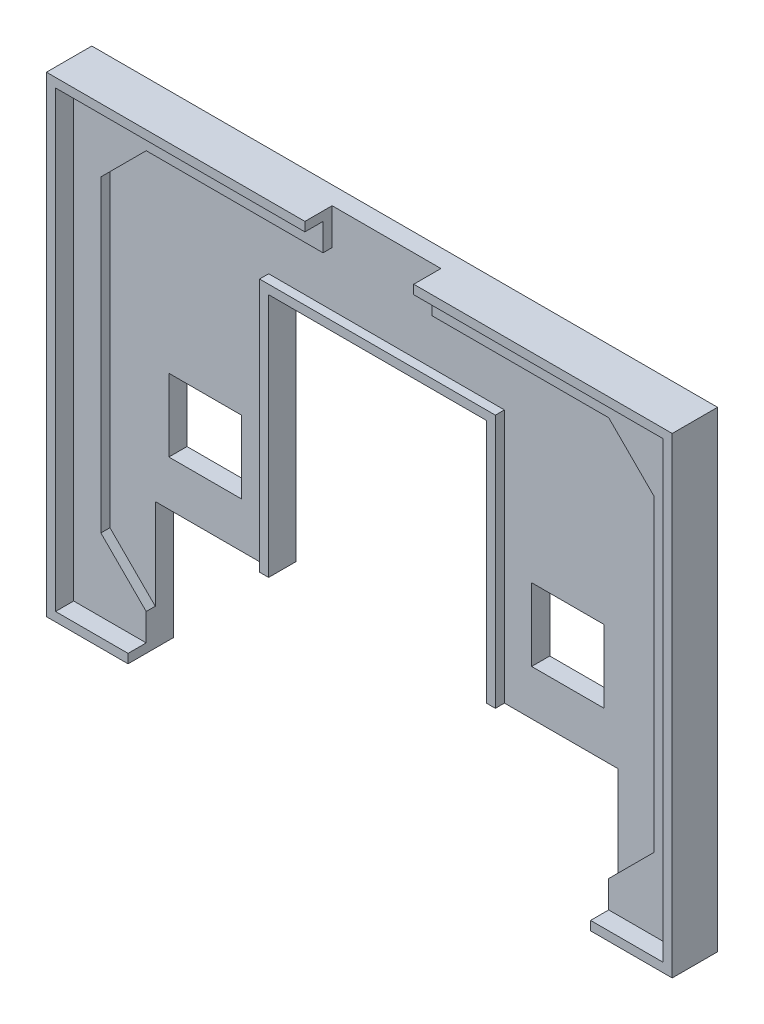
SolidWorks part; units mm, degrees
ref_plane "Přední rovina" through (0, 0, 0) normal (0, 0, 1) x (1, 0, 0)
ref_plane "Horní rovina" through (0, 0, 0) normal (0, 1, 0) x (1, 0, 0)
ref_plane "Pravá rovina" through (0, 0, 0) normal (1, 0, 0) x (0, 0, -1)
sketch "Skica1" plane through (0, 0, 0) normal (0, 0, 1) x (1, 0, 0)
  line L1 (-33.5, -25) -> (33.5, -25)
  line L2 (-33.5, -25) -> (-33.5, 25)
  line L3 (-33.5, 25) -> (33.5, 25)
  line L4 (33.5, -25) -> (33.5, 25)
  line L5 (-33.5, -25) -> (33.5, 25) construction
  line L6 (-33.5, 25) -> (33.5, -25) construction
  point P0 (0, 0)
  dimension "D1" = 67
  dimension "D2" = 50
extrude "Přidat vysunutím1" add sketch "Skica1" along normal blind 3
sketch "Skica2" plane through (0, 0, 3) normal (0, 0, 1) x (1, 0, 0)
  line L0 (-1000, 0) -> (49000, 0) construction
  line L1 (0, -1000) -> (0, 49000) construction
  line L2 (-1000, -22) -> (49000, -22) construction
  line L3 (-25.5, -1000) -> (-25.5, 49000) construction
  line L4 (-30.5, -1000) -> (-30.5, 49000) construction
  line L6 (-33.5, -25) -> (33.5, -25) construction
  line L7 (-25.5, -22) -> (-30.5, -17)
  line L8 (-30.5, -17) -> (-30.5, 17)
  line L9 (-25.5, -22) -> (25.5, -22)
  line L10 (30.5, -17) -> (30.5, 17)
  line L11 (25.5, -22) -> (30.5, -17)
  line L12 (25.5, 22) -> (30.5, 17)
  line L13 (-25.5, 22) -> (25.5, 22)
  line L14 (-25.5, 22) -> (-30.5, 17)
  point P20 (0, -22)
  point P21 (30.5, 0)
  point P24 (-30.5, 0)
  dimension "D1" = 30.5
  dimension "D2" = 5
  dimension "D3" = 3
  dimension "D4" = 45
extrude "Odebrat vysunutím1" cut sketch "Skica2" against normal offset from surface (1 mm away) 2 up to face at (0, 0, 0)
sketch "Skica3" plane through (0, 0, 0) normal (0, 0, -1) x (-1, 0, 0)
  line L0 (0, -1000) -> (0, 49000) construction
  line L1 (33.5, -25) -> (-33.5, -25) construction
  line L2 (24, 1) -> (16, 1)
  line L3 (24, 1) -> (24, -7)
  line L4 (24, -7) -> (16, -7)
  line L5 (16, 1) -> (16, -7)
  line L6 (-16, 1) -> (-16, -7)
  line L7 (33.5, -25) -> (-33.5, -25) construction
  line L8 (25.5, -25) -> (-25.5, -25)
  line L9 (25.5, -25) -> (25.5, -12)
  line L11 (-25.5, -25) -> (-25.5, -12)
  line L12 (-24, -7) -> (-16, -7)
  line L13 (25.5, -12) -> (12, -12)
  line L15 (12, -12) -> (12, 15)
  line L16 (12, 15) -> (-12, 15)
  line L17 (-12, -12) -> (-12, 15)
  line L18 (-12, -12) -> (-25.5, -12)
  line L19 (-24, 1) -> (-24, -7)
  line L20 (-24, 1) -> (-16, 1)
  dimension "D1" = 16
  dimension "D2" = 8
  dimension "D3" = 18
  dimension "D4" = 13
  dimension "D5" = 51
  dimension "D6" = 24
  dimension "D7" = 27
extrude "Odebrat vysunutím2" cut sketch "Skica3" against normal through all
sketch "Skica4" plane through (0, 0, 2) normal (0, 0, 1) x (1, 0, 0)
  line L0 (12, 15) -> (12, -12) construction
  line L1 (-12, -12) -> (-12, 15) construction
  line L2 (-12, 15) -> (12, 15) construction
  line L3 (12, 15) -> (12, -12)
  line L4 (-12, -12) -> (-12, 15)
  line L5 (-12, 15) -> (12, 15)
extrude "Vysunout tenkostěnný1" add sketch "Skica4" along normal up to surface (1 mm away) thin up to face at (0, -3.5714, 3) thin type one direction reverse wall 1
sketch "Skica5" plane through (0, 0, 0) normal (0, 0, -1) x (-1, 0, 0)
  line L0 (-33.5, 25) -> (33.5, 25) construction
  line L1 (33.5, 25) -> (33.5, -25) construction
  line L2 (33.5, -25) -> (25.5, -25) construction
  line L3 (-33.5, -25) -> (-33.5, 25) construction
  line L4 (-25.5, -25) -> (-33.5, -25) construction
  line L5 (-33.5, 25) -> (33.5, 25)
  line L6 (33.5, 25) -> (33.5, -25)
  line L7 (33.5, -25) -> (25.5, -25)
  line L8 (-33.5, -25) -> (-33.5, 25)
  line L9 (-25.5, -25) -> (-33.5, -25)
extrude "Vysunout tenkostěnný2" add sketch "Skica5" against normal blind 5 thin thin type one direction reverse wall 1
sketch "Skica6" plane through (0, 0, 2) normal (0, 0, 1) x (1, 0, 0)
  line L0 (0, -1000) -> (0, 49000) construction
  line L1 (25.5, 22) -> (-25.5, 22) construction
  line L2 (-6, 22) -> (6, 22)
  line L3 (-6, 22) -> (-6, 26)
  line L4 (-6, 26) -> (6, 26)
  line L5 (6, 22) -> (6, 26)
  line L6 (34.5, 26) -> (-34.5, 26) construction
  dimension "D1" = 12
extrude "Odebrat vysunutím3" cut sketch "Skica6" along normal through all
sketch "Skica7" plane through (0, 0, 0) normal (0, 0, -1) x (-1, 0, 0)
  line L0 (-412.4785, -204.4844) -> (-71.1451, -204.4844) construction
  line L1 (-32.44, 14.5405) -> (-23.4595, 23.94)
  line L2 (-23.4595, 23.94) -> (-14.06, 14.9595)
  line L3 (-14.06, 14.9595) -> (-23.0405, 5.56)
  line L4 (-23.0405, 5.56) -> (-32.44, 14.5405)
  line L5 (-34.5, 26) -> (34.5, 26) construction
  line L6 (0, 0) -> (0, 28.27) construction
  line L7 (-34.5, -26) -> (-34.5, 26) construction
  line L8 (14.06, 14.9595) -> (23.0405, 5.56)
  line L9 (23.4595, 23.94) -> (14.06, 14.9595)
  line L10 (32.44, 14.5405) -> (23.4595, 23.94)
  line L11 (23.0405, 5.56) -> (32.44, 14.5405)
  dimension "D1" = 13
  dimension "D2" = 13
  dimension "D3" = 2.06
  dimension "D4" = 2.06
  dimension "D5" = 2.06
extrude "Odebrat vysunutím5" cut sketch "Skica7" against normal blind 1
sketch "Skica8" plane through (0, 0, 0) normal (0, 0, -1) x (-1, 0, 0)
  line L4 (-32.44, 14.5405) -> (-23.0405, 5.56) construction
  line L5 (-23.4595, 23.94) -> (-32.44, 14.5405) construction
  line L10 (-14.06, 14.9595) -> (-23.4595, 23.94) construction
  line L16 (-32.44, 14.5405) -> (-23.0405, 5.56) construction
  line L17 (0, 0) -> (0, 28.374) construction
  line L30 (-29.2669, 14.9665) -> (-25.7669, 15.0801)
  line L31 (-23.7033, 17.2576) -> (-23.7476, 20.7576)
  line L47 (29.2669, 14.9665) -> (25.7669, 15.0801)
  line L48 (23.7033, 17.2576) -> (23.7476, 20.7576)
  spline S0 degree 2 poles (-29.2669, 14.9665) (-27.3984, 11.3649) (-25.7669, 15.0801) knots 0 0 0 1 1 1
  spline S1 degree 2 poles (-23.7033, 17.2576) (-20.0638, 19.0473) (-23.7476, 20.7576) knots 0 0 0 1 1 1
  spline S2 degree 2 poles (29.2669, 14.9665) (27.3984, 11.3649) (25.7669, 15.0801) knots 0 0 0 1 1 1
  spline S3 degree 2 poles (23.7033, 17.2576) (20.0638, 19.0473) (23.7476, 20.7576) knots 0 0 0 1 1 1
  dimension "D7" = 5.3
  dimension "D9" = 5.3
  dimension "D17" = 5
  dimension "D2" = 2.5
  dimension "D3" = 2
  dimension "D4" = 3.5
  dimension "D5" = 3.5
  dimension "D6" = 3
  dimension "D8" = 2.5
  dimension "D16" = 8
sketch "Skica11" plane through (0, 0, 0) normal (0, 0, -1) x (-1, 0, 0)
  line L0 (-25.7245, 9.2308) -> (-24.692, 9.8422)
  line L1 (-24.692, 9.8422) -> (-24.9875, 11.7191)
  line L2 (-24.9875, 11.7191) -> (-22.9908, 11.8342)
  line L3 (-22.9908, 11.8342) -> (-22.7446, 14.1209)
  line L4 (-22.7446, 14.1209) -> (-20.4484, 14.2532)
  line L5 (-20.4484, 14.2532) -> (-20.2342, 16.2418)
  line L6 (-20.2342, 16.2418) -> (-18.3342, 16.3512)
  line L7 (-18.3342, 16.3512) -> (-17.7987, 17.4251)
  line L8 (-17.7987, 17.4251) -> (-17.6541, 17.2869)
  line L9 (-17.6541, 17.2869) -> (-17.0373, 14.351)
  line L10 (-17.0373, 14.351) -> (-18.2373, 14.351)
  line L11 (-18.2373, 14.351) -> (-18.5958, 12.3834)
  line L12 (-18.5958, 12.3834) -> (-20.4614, 12.0232)
  line L13 (-20.4614, 12.0232) -> (-20.6648, 10.1341)
  line L14 (-20.6648, 10.1341) -> (-22.6285, 9.7549)
  line L15 (-22.6285, 9.7549) -> (-22.6285, 8.5549)
  line L16 (-22.6285, 8.5549) -> (-25.5799, 9.0927)
  line L17 (-25.5799, 9.0927) -> (-25.7245, 9.2308)
  line L18 (-14.06, 14.9595) -> (-23.4595, 23.94) construction
  line L19 (-23.0405, 5.56) -> (-14.06, 14.9595) construction
  line L20 (0, 0) -> (0, 28.2245) construction
  line L21 (-14.06, 14.9595) -> (-23.4595, 23.94) construction
  line L22 (-32.44, 14.5405) -> (-23.0405, 5.56) construction
  line L23 (-32.44, 14.5405) -> (-23.0405, 5.56) construction
  line L24 (-23.0405, 5.56) -> (-14.06, 14.9595) construction
  line L25 (22.6285, 8.5549) -> (25.5799, 9.0927)
  line L26 (22.6285, 9.7549) -> (22.6285, 8.5549)
  line L27 (20.6648, 10.1341) -> (22.6285, 9.7549)
  line L28 (20.4614, 12.0232) -> (20.6648, 10.1341)
  line L29 (18.5958, 12.3834) -> (20.4614, 12.0232)
  line L30 (18.2373, 14.351) -> (18.5958, 12.3834)
  line L31 (17.0373, 14.351) -> (18.2373, 14.351)
  line L32 (17.6541, 17.2869) -> (17.0373, 14.351)
  line L33 (17.7987, 17.4251) -> (17.6541, 17.2869)
  line L34 (18.3342, 16.3512) -> (17.7987, 17.4251)
  line L35 (20.2342, 16.2418) -> (18.3342, 16.3512)
  line L36 (20.4484, 14.2532) -> (20.2342, 16.2418)
  line L37 (22.7446, 14.1209) -> (20.4484, 14.2532)
  line L38 (22.9908, 11.8342) -> (22.7446, 14.1209)
  line L39 (24.9875, 11.7191) -> (22.9908, 11.8342)
  line L40 (24.692, 9.8422) -> (24.9875, 11.7191)
  line L41 (25.7245, 9.2308) -> (24.692, 9.8422)
  line L42 (25.5799, 9.0927) -> (25.7245, 9.2308)
  dimension "D1" = 0.8
  dimension "D2" = 0.8
  dimension "D3" = 0.8
  dimension "D4" = 0.8
  dimension "D5" = 1.2
  dimension "D6" = 1.2
  dimension "D7" = 1.9
  dimension "D8" = 1.9
  dimension "D9" = 2
  dimension "D10" = 2
  dimension "D11" = 2.3
  dimension "D12" = 2.3
  dimension "D13" = 1.9
  dimension "D14" = 1.9
  dimension "D15" = 2
  dimension "D16" = 2
  dimension "D17" = 1.2
  dimension "D18" = 1.2
  dimension "D19" = 3
  dimension "D20" = 3
  dimension "D21" = 2.6
  dimension "D22" = 2.6
  dimension "D23" = 2.6
  dimension "D24" = 1.5
  dimension "D25" = 5.7
  dimension "D26" = 5.35
  dimension "D27" = 0.2
  dimension "D28" = 0.2
extrude "Přidat vysunutím5" add sketch "Skica8" along normal blind 1 from offset 1 offset against normal yes
extrude "Přidat vysunutím6" add sketch "Skica11" along normal blind 1 from offset 1 offset against normal yes
sketch "Skica12" plane through (0, 0, 0) normal (0, 0, -1) x (-1, 0, 0)
  line L0 (-10.16, 23.3) -> (-6.3695, 23.3)
  line L1 (-6.3695, 23.3) -> (-6.3695, 22.5669)
  line L2 (-6.3695, 22.5669) -> (-5.7, 22.5669)
  line L3 (-5.7, 22.5669) -> (-5.7, 20.7747)
  line L4 (-5.7, 20.7747) -> (-6.3472, 20.7747)
  line L5 (-6.3472, 20.7747) -> (-6.3472, 20.0778)
  line L6 (-6.3472, 20.0778) -> (-6.9446, 20.0778)
  line L7 (-6.9446, 20.0778) -> (-6.9446, 19.5467)
  line L8 (-6.9446, 19.5467) -> (-6.3472, 19.5467)
  line L9 (-6.3472, 19.5467) -> (-6.3472, 18.7336)
  line L10 (-6.3472, 18.7336) -> (-5.7, 18.7336)
  line L11 (-5.7, 18.7336) -> (-5.7, 17.8043)
  line L12 (-5.7, 17.8043) -> (-7.1437, 17.8043)
  line L13 (-7.1437, 17.8043) -> (-7.1437, 18.5013)
  line L14 (-7.1437, 18.5013) -> (-7.7743, 18.5013)
  line L15 (-7.7743, 18.5013) -> (-7.7743, 19.1402)
  line L16 (-7.7743, 19.1402) -> (-8.2536, 19.1402)
  line L17 (-8.2536, 19.1402) -> (-8.2536, 20.0778)
  line L18 (-8.2536, 20.0778) -> (-8.77, 20.0778)
  line L19 (-8.77, 20.0778) -> (-8.77, 17.8043)
  line L20 (-8.77, 17.8043) -> (-10.16, 17.8043)
  line L21 (-10.16, 17.8043) -> (-10.16, 23.3)
  line L22 (-4.9366, 23.3) -> (-3.432, 23.3)
  line L23 (-3.432, 23.3) -> (-3.432, 18.7336)
  line L24 (-3.432, 18.7336) -> (-1.8153, 18.7336)
  line L25 (-1.8153, 18.7336) -> (-1.8153, 23.3)
  line L26 (-1.8153, 23.3) -> (-0.3525, 23.3)
  line L27 (-0.3525, 23.3) -> (-0.3525, 18.5013)
  line L28 (-0.3525, 18.5013) -> (-1.0728, 18.5013)
  line L29 (-1.0728, 18.5013) -> (-1.0728, 17.8043)
  line L30 (-1.0728, 17.8043) -> (-4.2581, 17.8043)
  line L31 (-4.2581, 17.8043) -> (-4.2581, 18.5013)
  line L32 (-4.2581, 18.5013) -> (-4.9366, 18.5013)
  line L33 (-4.9366, 18.5013) -> (-4.9366, 23.3)
  line L34 (4.306, 22.5669) -> (4.9679, 22.5669)
  line L35 (4.9679, 22.5669) -> (4.9679, 21.5831)
  line L36 (4.9679, 21.5831) -> (3.38, 21.5831)
  line L37 (3.38, 21.5831) -> (3.38, 22.2558)
  line L38 (3.38, 22.2558) -> (1.9024, 22.2558)
  line L39 (1.9024, 22.2558) -> (1.9024, 21.0168)
  line L40 (1.9024, 21.0168) -> (4.2511, 21.0168)
  line L41 (4.2511, 21.0168) -> (4.2511, 20.304)
  line L42 (4.2511, 20.304) -> (4.9679, 20.304)
  line L43 (4.9679, 20.304) -> (4.9679, 18.5013)
  line L44 (4.9679, 18.5013) -> (4.2511, 18.5013)
  line L45 (4.2511, 18.5013) -> (4.2511, 17.8043)
  line L46 (4.2511, 17.8043) -> (1.0313, 17.8043)
  line L47 (1.0313, 17.8043) -> (1.0313, 18.5013)
  line L48 (1.0313, 18.5013) -> (0.4248, 18.5013)
  line L49 (0.4248, 18.5013) -> (0.4248, 19.5467)
  line L50 (0.4248, 19.5467) -> (1.9024, 19.5467)
  line L51 (1.9024, 19.5467) -> (1.9024, 18.8207)
  line L52 (1.9024, 18.8207) -> (3.4682, 18.8207)
  line L53 (3.4682, 18.8207) -> (3.4682, 20.0778)
  line L54 (3.4682, 20.0778) -> (1.0313, 20.0778)
  line L55 (1.0313, 20.0778) -> (1.0313, 20.7747)
  line L56 (1.0313, 20.7747) -> (0.4248, 20.7747)
  line L57 (0.4248, 20.7747) -> (0.4248, 22.5669)
  line L58 (0.4248, 22.5669) -> (1.0313, 22.5669)
  line L59 (1.0313, 22.5669) -> (1.0313, 23.3)
  line L60 (1.0313, 23.3) -> (4.306, 23.3)
  line L61 (4.306, 23.3) -> (4.306, 22.5669)
  line L62 (5.6728, 23.3) -> (7.1738, 23.3)
  line L63 (7.1738, 23.3) -> (7.1738, 21.0794)
  line L64 (7.1738, 21.0794) -> (8.7642, 21.0794)
  line L65 (8.7642, 21.0794) -> (8.7642, 23.3)
  line L66 (8.7642, 23.3) -> (10.158, 23.3)
  line L67 (10.158, 23.3) -> (10.158, 17.8043)
  line L68 (10.158, 17.8043) -> (8.7642, 17.8043)
  line L69 (8.7642, 17.8043) -> (8.7642, 20.0778)
  line L70 (8.7642, 20.0778) -> (7.1738, 20.0778)
  line L71 (7.1738, 20.0778) -> (7.1738, 17.8043)
  line L72 (7.1738, 17.8043) -> (5.6728, 17.8043)
  line L73 (5.6728, 17.8043) -> (5.6728, 23.3)
  line L74 (-34.5, 26) -> (34.5, 26) construction
  line L75 (-12, 15) -> (-12, -12) construction
  line L77 (-34.5, -26) -> (-34.5, 26) construction
  line L78 (-25.5, -26) -> (-34.5, -26) construction
  dimension "D1" = 2.7
  dimension "D2" = 1.84
  dimension "D3" = 9
  dimension "D4" = 25.73
  dimension "D5" = 26.2464
  dimension "D6" = 26.7257
  dimension "D7" = 27.3563
  dimension "D8" = 27.5554
  dimension "D9" = 28.1305
  dimension "D10" = 28.1528
  dimension "D11" = 28.8
  dimension "D12" = 29.5634
  dimension "D13" = 30.2419
  dimension "D14" = 31.068
  dimension "D15" = 32.6847
  dimension "D16" = 33.4272
  dimension "D17" = 34.1475
  dimension "D18" = 34.9248
  dimension "D19" = 35.5313
  dimension "D20" = 36.4024
  dimension "D21" = 43.8043
  dimension "D22" = 37.9682
  dimension "D23" = 38.7511
  dimension "D24" = 38.806
  dimension "D25" = 39.4679
  dimension "D26" = 40.1728
  dimension "D27" = 41.6738
  dimension "D28" = 43.2642
  dimension "D29" = 44.658
  dimension "D30" = 44.5013
  dimension "D31" = 44.7336
  dimension "D32" = 44.8207
  dimension "D33" = 45.1402
  dimension "D34" = 45.5467
  dimension "D35" = 46.0778
  dimension "D36" = 46.304
  dimension "D38" = 47.0168
  dimension "D39" = 47.0794
  dimension "D40" = 47.5831
  dimension "D41" = 48.2558
  dimension "D42" = 48.5669
  dimension "D43" = 52
extrude "Odebrat vysunutím6" cut sketch "Skica12" against normal blind 1
sketch "Skica13" plane through (0, 0, 0) normal (0, 0, -1) x (-1, 0, 0)
  line L1 (-8.77, 22.5669) -> (-6.9446, 22.5669)
  line L2 (-8.77, 22.5669) -> (-8.77, 20.7747)
  line L3 (-8.77, 20.7747) -> (-6.9446, 20.7747)
  line L4 (-6.9446, 22.5669) -> (-6.9446, 20.7747)
  line L5 (-5.7, 22.5669) -> (-6.3695, 22.5669) construction
  line L6 (-6.3472, 20.7747) -> (-5.7, 20.7747) construction
  line L7 (-8.77, 17.8043) -> (-8.77, 20.0778) construction
  line L10 (-6.9446, 19.5467) -> (-6.9446, 20.0778) construction
  dimension "D1" = 0
  dimension "D2" = 0
  dimension "D3" = 0
  dimension "D4" = 0
extrude "Přidat vysunutím7" add sketch "Skica13" along normal blind 1 from offset 1 offset against normal yes
